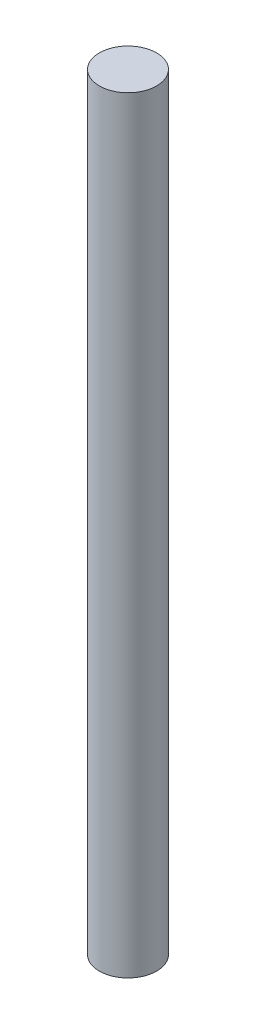
SolidWorks part; units mm, degrees
material "Hexcel AS4C (3000 Filaments)"
ref_plane "Front Plane" through (0, 0, 0) normal (0, 0, 1) x (1, 0, 0)
ref_plane "Top Plane" through (0, 0, 0) normal (0, 1, 0) x (1, 0, 0)
ref_plane "Right Plane" through (0, 0, 0) normal (1, 0, 0) x (0, 0, -1)
sketch "Sketch1" plane through (0, 0, 0) normal (0, 1, 0) x (1, 0, 0)
  circle A0 centre (0, 0) radius 1
  dimension "D1" = 2
extrude "Boss-Extrude1" add sketch "Sketch1" along normal mid plane 26.76
